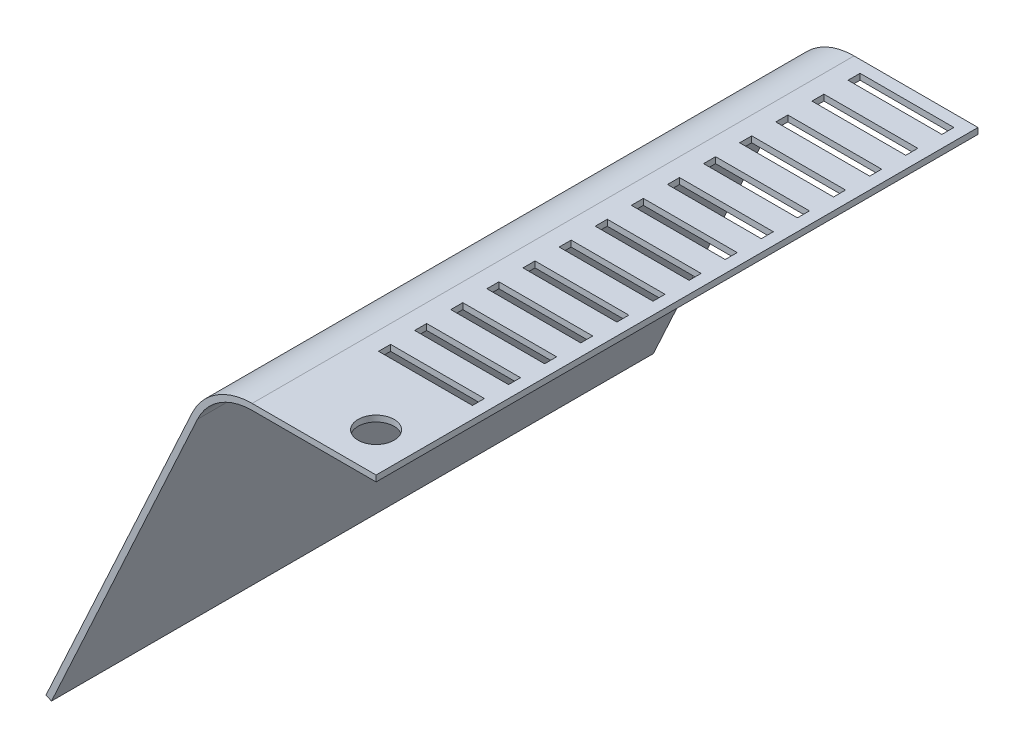
SolidWorks part; units mm, degrees
ref_plane "Front Plane" through (0, 0, 0) normal (0, 0, 1) x (1, 0, 0)
ref_plane "Top Plane" through (0, 0, 0) normal (0, 1, 0) x (1, 0, 0)
ref_plane "Right Plane" through (0, 0, 0) normal (1, 0, 0) x (0, 0, -1)
sketch "Sketch1" plane through (0, 0, 0) normal (0, 0, 1) x (1, 0, 0)
  line L0 (0, 0) -> (-205.95, 0)
  line L1 (-296.7862, -58.1816) -> (-539.333, -585.0317)
  arc A0 (-205.95, 0) -> (-296.7862, -58.1816) centre (-205.95, -100) ccw
  dimension "D1" = 100
  dimension "D2" = 205.95
  dimension "D3" = 114.72
  dimension "D4" = 580
extrude "Extrude-Thin1" add sketch "Sketch1" along normal mid plane 1000 thin
sketch "Sketch2" plane through (0, 10, 0) normal (0, 1, 0) x (1, 0, 0)
  line L0 (0, -500) -> (0, 500) construction
  line L1 (-175.95, 480) -> (-20, 480)
  line L2 (-175.95, 480) -> (-175.95, 460)
  line L3 (-175.95, 460) -> (-20, 460)
  line L4 (-20, 480) -> (-20, 460)
  line L5 (-175.95, 480) -> (-20, 460) construction
  line L6 (-175.95, 460) -> (-20, 480) construction
  line L7 (0, 500) -> (-205.95, 500) construction
  line L8 (-205.95, -500) -> (-205.95, 500) construction
  point P0 (-97.975, 470)
  dimension "D1" = 20
  dimension "D2" = 20
  dimension "D3" = 20
  dimension "D4" = 30
extrude "Cut-Extrude1" cut sketch "Sketch2" against normal through all
pattern_linear "LPattern1" count 14 spacing 60 along (0, 0, 1) of "Cut-Extrude1"
sketch "Sketch3" plane through (0, 10, 0) normal (0, 1, 0) x (1, 0, 0)
  line L0 (0, -500) -> (-205.95, -500) construction
  line L1 (0, -500) -> (0, 500) construction
  circle A0 centre (-65, -435) radius 30
  dimension "D3" = 60
  dimension "D1" = 65
  dimension "D2" = 65
extrude "Cut-Extrude2" cut sketch "Sketch3" against normal through all
